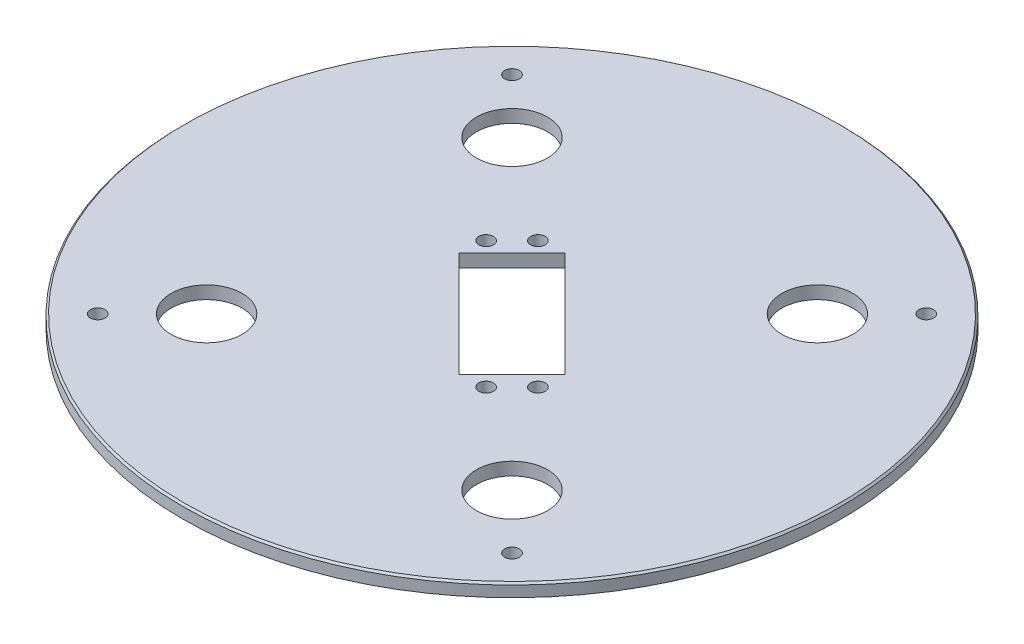
SolidWorks part; units mm, degrees
ref_plane "Front Plane" through (0, 0, 0) normal (0, 0, 1) x (1, 0, 0)
ref_plane "Top Plane" through (0, 0, 0) normal (0, 1, 0) x (1, 0, 0)
ref_plane "Right Plane" through (0, 0, 0) normal (1, 0, 0) x (0, 0, -1)
sketch "Sketch1" plane through (0, 0, 0) normal (0, 1, 0) x (1, 0, 0)
  line L0 (0, 0) -> (0, 41.7) construction
  line L1 (0, 41.7) -> (-32, 41.7) construction
  line L2 (-41.7, 32) -> (-41.7, 0) construction
  line L3 (-41.7, 0) -> (0, 0) construction
  line L4 (0, 0) -> (-63.6396, 63.6396) construction
  line L5 (7.1418, -21.6375) -> (-21.6375, 7.1418)
  line L6 (7.1418, -21.6375) -> (21.6375, -7.1418)
  line L7 (-21.6375, 7.1418) -> (-7.1418, 21.6375)
  line L8 (21.6375, -7.1418) -> (-7.1418, 21.6375)
  line L9 (7.1418, -21.6375) -> (-7.1418, 21.6375) construction
  line L10 (-21.6375, 7.1418) -> (21.6375, -7.1418) construction
  line L12 (14.3896, -14.3896) -> (-14.3896, 14.3896) construction
  line L13 (-7.2478, -7.2478) -> (7.2478, 7.2478) construction
  circle A0 centre (0, 0) radius 90
  circle A1 centre (-41.7, 41.7) radius 9.7
  circle A2 centre (41.7, 41.7) radius 9.7
  circle A3 centre (41.7, -41.7) radius 9.7
  circle A4 centre (-41.7, -41.7) radius 9.7
  circle A5 centre (-56.5685, 56.5685) radius 2
  circle A6 centre (-56.5685, -56.5685) radius 2
  circle A7 centre (56.5685, 56.5685) radius 2
  circle A8 centre (56.5685, -56.5685) radius 2
  circle A17 centre (-13.7886, 20.8597) radius 2
  circle A19 centre (20.8597, -13.7886) radius 2
  circle A20 centre (13.7886, -20.8597) radius 2
  circle A21 centre (-20.8597, 13.7886) radius 2
  point P5 (-32, 41.7)
  point P10 (-41.7, 32)
  dimension "D1" = 32
  dimension "D2" = 19.4
  dimension "D4" = 180
  dimension "D6" = 4
  dimension "D9" = 20.5
  dimension "D10" = 4
  dimension "D3" = 32
  dimension "D5" = 45
  dimension "D7" = 10
  dimension "D8" = 40.7
  dimension "D11" = 49
  dimension "D12" = 10
extrude "Boss-Extrude1" add sketch "Sketch1" along normal blind 3.5
chamfer "Chamfer1" distance 0.5 angle 45 1 edges at (0, 3.5, 90)
